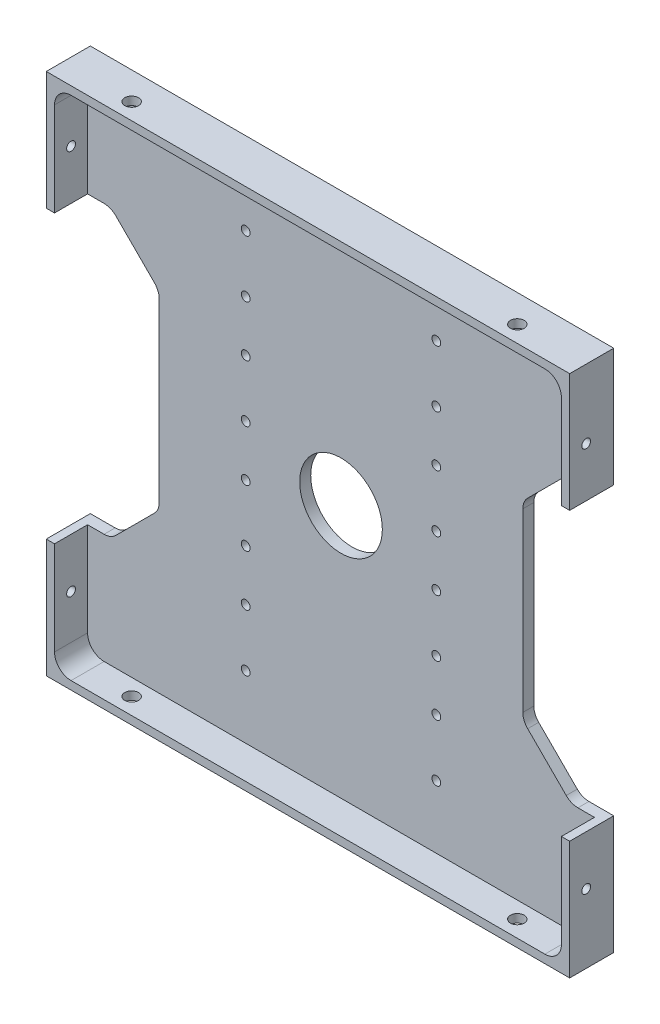
SolidWorks part; units mm, degrees
material "6061-T6 (SS)"
ref_plane "Front" through (0, 0, 0) normal (0, 0, 1) x (1, 0, 0)
ref_plane "Top" through (0, 0, 0) normal (0, 1, 0) x (1, 0, 0)
ref_plane "Right" through (0, 0, 0) normal (1, 0, 0) x (0, 0, -1)
sketch "Sketch1" plane through (0, 0, 0) normal (0, 0, 1) x (1, 0, 0)
  line L1 (-48, -48) -> (48, -48)
  line L2 (-48, -48) -> (-48, 48)
  line L3 (-48, 48) -> (48, 48)
  line L4 (48, -48) -> (48, 48)
  line L5 (-48, -48) -> (48, 48) construction
  line L6 (-48, 48) -> (48, -48) construction
  point P0 (0, 0)
  dimension "D1" = 96
  dimension "D2" = 96
extrude "Boss-Extrude1" add sketch "Sketch1" along normal blind 8
sketch "Sketch2" plane through (0, 0, 8) normal (0, 0, 1) x (1, 0, 0)
  line L1 (46, -46) -> (-46, -46)
  line L2 (46, -46) -> (46, 46)
  line L3 (46, 46) -> (-46, 46)
  line L4 (-46, -46) -> (-46, 46)
  line L5 (46, -46) -> (-46, 46) construction
  line L6 (46, 46) -> (-46, -46) construction
  point P0 (0, 0)
  dimension "D1" = 92
  dimension "D2" = 92
extrude "Component Platform" cut sketch "Sketch2" against normal blind 6
sketch "Sketch3" plane through (0, 0, 2) normal (0, 0, 1) x (1, 0, 0)
  line L1 (-40.8787, -25.1213) -> (-33.8787, -18.1213)
  line L2 (-40.8787, 25.1213) -> (-33.8787, 18.1213)
  line L3 (-33, -16) -> (-33, 16)
  line L4 (-48, -26) -> (-43, -26)
  line L7 (-48, 48) -> (-48, -48) construction
  line L8 (0, -56.7987) -> (0, 73.4321) construction
  line L9 (46, -46) -> (-57.8147, 57.8147) construction
  line L18 (46, 46) -> (-68.5705, -68.5705) construction
  line L23 (-48, 26) -> (-43, 26)
  line L26 (-48, -26) -> (-48, 26)
  line L28 (-48, -48) -> (48, -48) construction
  line L29 (48, -26) -> (48, 26)
  line L30 (48, 26) -> (43, 26)
  line L31 (40.8787, 25.1213) -> (33.8787, 18.1213)
  line L32 (33, -16) -> (33, 16)
  line L33 (40.8787, -25.1213) -> (33.8787, -18.1213)
  line L34 (48, -26) -> (43, -26)
  arc A3 (-33.8787, -18.1213) -> (-33, -16) centre (-36, -16) ccw
  arc A4 (-33.8787, 18.1213) -> (-33, 16) centre (-36, 16) cw
  arc A13 (-40.8787, -25.1213) -> (-43, -26) centre (-43, -23) cw
  arc A15 (-40.8787, 25.1213) -> (-43, 26) centre (-43, 23) ccw
  arc A17 (40.8787, 25.1213) -> (43, 26) centre (43, 23) cw
  arc A18 (33.8787, 18.1213) -> (33, 16) centre (36, 16) ccw
  arc A19 (33.8787, -18.1213) -> (33, -16) centre (36, -16) cw
  arc A20 (40.8787, -25.1213) -> (43, -26) centre (43, -23) ccw
  point P0 (-48, 0)
  point P37 (-48, 0)
  dimension "D2" = 3
  dimension "D3" = 3
  dimension "D4" = 15
  dimension "D6" = 3
  dimension "D7" = 3
  dimension "D8" = 135
  dimension "D5" = 52
  dimension "D9" = 135
  dimension "D10" = 5
  dimension "D11" = 5
  dimension "D12" = 48
extrude "Cable Slots" cut sketch "Sketch3" against normal mid plane 12
sketch "Sketch4" plane through (0, 0, 2) normal (0, 0, 1) x (1, 0, 0)
  circle A0 centre (0, 0) radius 7.5
  dimension "D1" = 15
extrude "Center Mass Cut" cut sketch "Sketch4" against normal blind 6
ref_plane "Center Y-Plane" through (0, 0, 0) normal (1, 0, 0) x (0, 0, -1)
ref_plane "Center X-Plane" through (0, 0, 0) normal (0, -1, 0) x (-1, 0, 0)
fillet "Inner Corner Fillets" radius 3 4 edges at (46, -46, 5) (-46, -46, 5) (46, 46, 5) (-46, 46, 5)
sketch "Sketch8" plane through (48, 0, 0) normal (1, 0, 0) x (0, 0, -1)
  line L0 (-5, -48) -> (-5, 48) construction
  line L1 (-8, -48) -> (0, -48) construction
  line L2 (-8, 48) -> (0, 48) construction
  line L3 (-8, -48) -> (-8, -26) construction
  point P12 (-5, 35)
  point P13 (-5, -35)
  dimension "D1" = 3
  dimension "D2" = 13
  dimension "D3" = 83
sketch "Sketch11" plane through (0, -48, 0) normal (0, -1, 0) x (-1, 0, 0)
  line L0 (48, -5) -> (-48.0639, -5) construction
  line L1 (48, -8) -> (48, 0) construction
  line L2 (48, -8) -> (-48, -8) construction
  dimension "D1" = 3
hole_wizard "Tap Drill for M3x0.5 Tap4" positions "Sketch12" profile "Sketch13" hole size "M3x0.5" standard "ANSI Metric" end condition up to next
sketch "Sketch12" plane through (0, -48, 0) normal (0, -1, 0) x (-1, 0, 0)
  line L0 (48, -5) -> (-48.0639, -5) construction
  point P0 (35, -5)
  point P4 (-35, -5)
  dimension "D1" = 70
  dimension "D2" = 35
sketch "Sketch13" plane through (-35, -48, 5) normal (1, 0, 0) x (0, 0, -1)
  line L0 (0, 0) -> (0, 2)
  line L1 (0, 2) -> (1.25, 2)
  line L2 (1.25, 2) -> (1.25, 0)
  line L5 (1.25, 0) -> (0, 0)
  line L11 (0, -6.35) -> (0, 107.95) construction
  dimension "Thru Hole Dia." = 2.5
  dimension "Thru Hole Depth" = 2
mirror "Mirror2" about plane through (0, 0, 0) normal (0, -1, 0) of "Tap Drill for M3x0.5 Tap4"
sketch "Sketch14" plane through (0, 0, 2) normal (0, 0, 1) x (1, 0, 0)
  line L2 (-34.5286, 34.575) -> (20.3487, 34.575) construction
  line L4 (-17.3, 34.575) -> (-17.3, -34.575) construction
  line L5 (0, 0) -> (0, 34.575) construction
  point P2 (-17.3, -14.975)
  point P5 (-17.3, -4.625)
  point P7 (-17.3, 34.575)
  point P8 (-17.3, 14.975)
  point P9 (-17.3, 24.225)
  point P11 (-17.3, 4.625)
  point P13 (17.3, 4.625)
  point P14 (17.3, 14.975)
  point P15 (17.3, 24.225)
  point P16 (17.3, 34.575)
  point P17 (-17.3, -24.225)
  point P18 (-17.3, -34.575)
  point P30 (17.3, -34.575)
  point P31 (17.3, -24.225)
  point P32 (17.3, -14.975)
  point P33 (17.3, -4.625)
  point P35 (-17.3, 0)
  dimension "D1" = 17.3
  dimension "D3" = 10.35
  dimension "D4" = 9.25
  dimension "D5" = 10.35
  dimension "D6" = 9.25
  dimension "D7" = 10.35
  dimension "D8" = 9.25
  dimension "D9" = 10.35
hole_wizard "Tap Drill for M2x0.4 Tap2" positions "Sketch15" profile "Sketch17" hole size "M2x0.4" standard "ANSI Metric" end condition through all
sketch "Sketch15" plane through (0, 0, 2) normal (0, 0, 1) x (1, 0, 0)
  point P0 (-17.3, 34.575)
  point P3 (-17.3, 24.225)
  point P6 (-17.3, 14.975)
  point P9 (-17.3, 4.625)
  point P12 (17.3, 4.625)
  point P15 (17.3, 14.975)
  point P18 (17.3, 24.225)
  point P21 (17.3, 34.575)
  point P46 (17.3, -4.625)
  point P49 (17.3, -14.975)
  point P52 (17.3, -24.225)
  point P55 (17.3, -34.575)
  point P58 (-17.3, -4.625)
  point P61 (-17.3, -14.975)
  point P64 (-17.3, -24.225)
  point P67 (-17.3, -34.575)
sketch "Sketch17" plane through (-17.3, 34.575, 2) normal (1, 0, 0) x (0, -1, 0)
  line L0 (0, 0) -> (0, 2)
  line L1 (0, 2) -> (0.8, 2)
  line L2 (0.8, 2) -> (0.8, 0)
  line L5 (0.8, 0) -> (0, 0)
  line L11 (0, -6.35) -> (0, 107.95) construction
  dimension "Thru Hole Dia." = 1.6
  dimension "Thru Hole Depth" = 2
hole_wizard "Tap Drill for M2x0.4 Tap1" positions "Sketch26" profile "Sketch27" hole size "M2x0.4" standard "ANSI Metric" end condition up to next
sketch "Sketch26" plane through (48, 0, 0) normal (1, 0, 0) x (0, 0, -1)
  point P0 (-5, -35)
  point P3 (-5, 35)
sketch "Sketch27" plane through (48, -35, 5) normal (0, 1, 0) x (0, 0, -1)
  line L0 (0, 0) -> (0, 2)
  line L1 (0, 2) -> (0.8, 2)
  line L2 (0.8, 2) -> (0.8, 0)
  line L5 (0.8, 0) -> (0, 0)
  line L11 (0, -6.35) -> (0, 107.95) construction
  dimension "Thru Hole Dia." = 1.6
  dimension "Thru Hole Depth" = 2
mirror "Mirror3" about plane through (0, 0, 0) normal (1, 0, 0) of "Tap Drill for M2x0.4 Tap1"
sketch "Sketch28" plane through (0, 0, 0) normal (0, 0, -1) x (-1, 0, 0)
  line L1 (47.5, -47.5) -> (-47.5, -47.5)
  line L2 (47.5, -47.5) -> (47.5, 47.5)
  line L3 (47.5, 47.5) -> (-47.5, 47.5)
  line L4 (-47.5, -47.5) -> (-47.5, 47.5)
  line L5 (47.5, -47.5) -> (-47.5, 47.5) construction
  line L6 (47.5, 47.5) -> (-47.5, -47.5) construction
  point P0 (0, 0)
  dimension "D1" = 95
  dimension "D2" = 95
extrude "Cut-Extrude1" cut sketch "Sketch28" against normal up to next flip side to cut
equation "\"MountingBracketXYSideTolerance\"= - 0.5"
equation "\"D2@Sketch28\"=96mm + \"MountingBracketXYSideTolerance\"*2"
equation "\"D1@Sketch28\"=96.00mm+\"MountingBracketXYSideTolerance\"*2"
